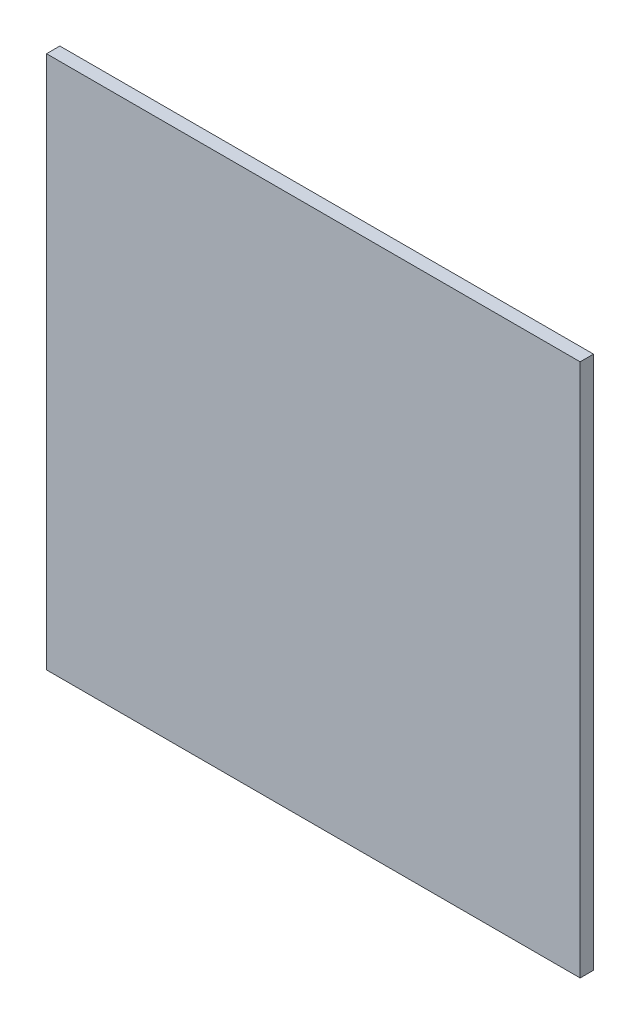
SolidWorks part; units mm, degrees
ref_plane "Front Plane" through (0, 0, 0) normal (0, 0, 1) x (1, 0, 0)
ref_plane "Top Plane" through (0, 0, 0) normal (0, 1, 0) x (1, 0, 0)
ref_plane "Right Plane" through (0, 0, 0) normal (1, 0, 0) x (0, 0, -1)
sketch "Esquisse1" plane through (0, 0, 0) normal (0, 0, 1) x (1, 0, 0)
  line L1 (-200, 200) -> (200, 200)
  line L2 (-200, 200) -> (-200, -200)
  line L3 (-200, -200) -> (200, -200)
  line L4 (200, 200) -> (200, -200)
  point P5 (-200, 0)
  point P7 (0, 200)
  dimension "D1" = 400
  dimension "D2" = 400
extrude "Boss.-Extru.1" add sketch "Esquisse1" along normal blind 10
